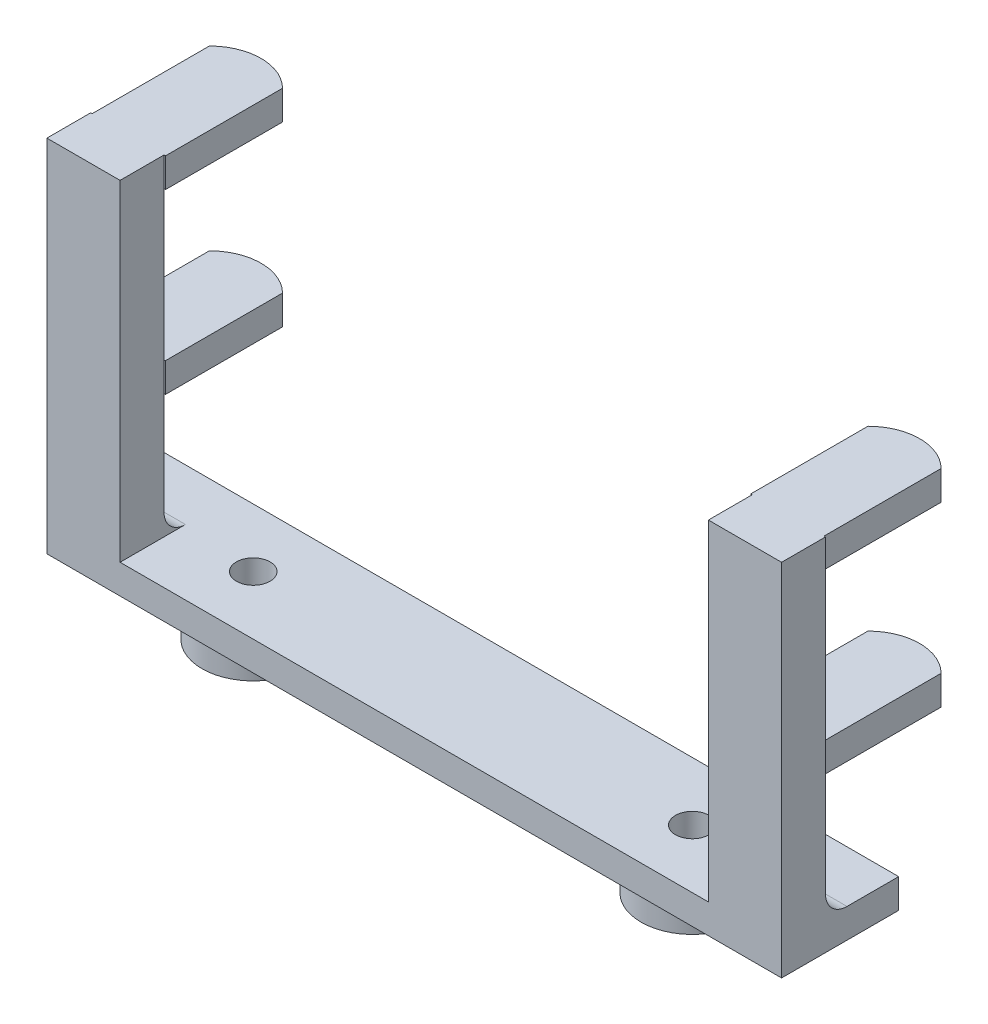
SolidWorks part; units mm, degrees
ref_plane "Front Plane" through (0, 0, 0) normal (0, 0, 1) x (1, 0, 0)
ref_plane "Top Plane" through (0, 0, 0) normal (0, 1, 0) x (1, 0, 0)
ref_plane "Right Plane" through (0, 0, 0) normal (1, 0, 0) x (0, 0, -1)
sketch "Sketch1" plane through (0, 0, 0) normal (0, 0, 1) x (1, 0, 0)
  line L0 (0, 0) -> (0, 17.4229) construction
  line L1 (25.527, 0) -> (-25.527, 0)
  line L2 (-25.527, 0) -> (-25.527, 28.702)
  line L3 (-20.0796, 28.702) -> (-9.5655, 28.702) construction
  line L4 (-25.527, 28.702) -> (-31.877, 28.702)
  line L5 (-31.877, 28.702) -> (-31.877, -2.54)
  line L6 (-31.877, -2.54) -> (31.877, -2.54)
  line L7 (25.527, 0) -> (25.527, 28.702)
  line L8 (25.527, 28.702) -> (31.877, 28.702)
  line L9 (31.877, 28.702) -> (31.877, -2.54)
  point P11 (0, -2.54)
  dimension "D1" = 28.702
  dimension "D2" = 25.527
  dimension "D3" = 2.54
  dimension "D4" = 6.35
extrude "Boss-Extrude1" add sketch "Sketch1" along normal blind 10.16
sketch "Sketch2" plane through (31.877, 0, 0) normal (1, 0, 0) x (0, 0, -1)
  line L3 (-6.35, 28.702) -> (-6.35, 1.8674)
  line L4 (-10.16, 28.702) -> (0, 28.702) construction
  line L5 (-4.4826, 0) -> (0, 0)
  line L6 (0, 0) -> (0, 28.702)
  line L8 (0, 28.702) -> (-6.35, 28.702)
  arc A0 (-6.35, 1.8674) -> (-4.4826, 0) centre (-4.4826, 1.8674) ccw
  point P0 (-10.16, -2.54)
  dimension "D1" = 6.35
extrude "Cut-Extrude1" cut sketch "Sketch2" against normal through all
sketch "Sketch3" plane through (0, -2.54, 0) normal (0, -1, 0) x (1, 0, 0)
  line L0 (0, -10.3156) -> (0, 44.934) construction
  circle A0 centre (-19.05, 5.08) radius 1.4605
  circle A1 centre (19.05, 5.08) radius 1.4605
  dimension "D1" = 38.1
  dimension "D2" = 2.921
extrude "Cut-Extrude2" cut sketch "Sketch3" against normal blind 6.35
sketch "Sketch5" plane through (0, 28.702, 0) normal (0, 1, 0) x (1, 0, 0)
  line L0 (-31.75, -6.35) -> (-31.75, 3.81)
  line L1 (-25.4, -6.35) -> (-25.4, 3.81)
  line L2 (-31.75, -6.35) -> (-25.4, -6.35)
  line L3 (-31.877, -6.35) -> (-25.527, -6.35) construction
  arc A0 (-31.75, 3.81) -> (-25.4, 3.81) centre (-28.575, 0.635) cw
  dimension "D1" = 10.16
  dimension "D2" = 10.16
extrude "Boss-Extrude2" add sketch "Sketch5" against normal blind 2.54
ref_plane "Plane1" through (0, 19.7358, 0) normal (0, -1, 0) x (-1, 0, 0)
mirror "Mirror1" about plane through (0, 19.7358, 0) normal (0, -1, 0) of "Boss-Extrude2"
mirror "Mirror2" about plane through (0, 0, 0) normal (1, 0, 0) of "Boss-Extrude2", "Mirror1"
sketch "Sketch6" plane through (0, -2.54, 0) normal (0, -1, 0) x (1, 0, 0)
  line L0 (0, -2.2614) -> (0, 14.8608) construction
  circle A0 centre (-19.05, 5.08) radius 4.445
  circle A1 centre (-19.05, 5.08) radius 1.4605
  circle A2 centre (19.05, 5.08) radius 1.4605
  circle A3 centre (19.05, 5.08) radius 4.445
  dimension "D1" = 2.921
  dimension "D2" = 8.89
extrude "Boss-Extrude3" add sketch "Sketch6" along normal blind 2.54
